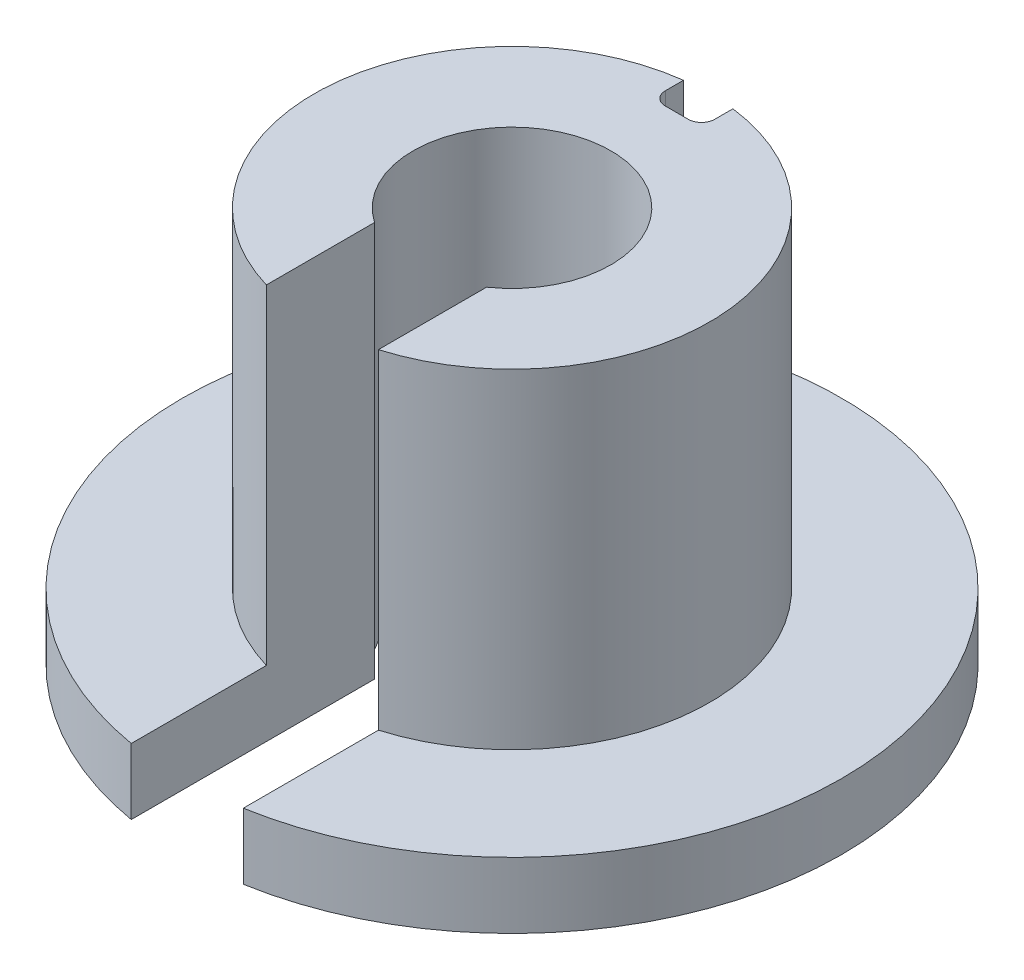
SolidWorks part; units mm, degrees
ref_plane "Front Plane" through (0, 0, 0) normal (0, 0, 1) x (1, 0, 0)
ref_plane "Top Plane" through (0, 0, 0) normal (0, 1, 0) x (1, 0, 0)
ref_plane "Right Plane" through (0, 0, 0) normal (1, 0, 0) x (0, 0, -1)
sketch "Sketch1" plane through (0, 0, 0) normal (0, 1, 0) x (1, 0, 0)
  line L0 (0, 0) -> (0, -6.8016) construction
  line L2 (-1.7, -2.4718) -> (-1.7, -5.7541)
  line L4 (1.7, -2.4718) -> (1.7, -5.7541)
  arc A0 (1.7, -2.4718) -> (-1.7, -2.4718) centre (0, 0) ccw
  arc A1 (1.7, -5.7541) -> (-1.7, -5.7541) centre (0, 0) ccw
  circle A3 centre (0, 0) radius 3 construction
  circle A4 centre (0, 0) radius 6 construction
  point P1 (5.7378, 1.7542)
  point P8 (2.8689, 0.8771)
  dimension "D1" = 6
  dimension "D3" = 1.7
  dimension "D4" = 1.7
  dimension "D2" = 3
extrude "Boss-Extrude1" add sketch "Sketch1" along normal blind 12
sketch "Sketch2" plane through (0, 0, 0) normal (0, -1, 0) x (1, 0, 0)
  line L0 (-1.7, 5.7541) -> (-1.7, 9.8544)
  line L2 (1.7, 5.7541) -> (1.7, 9.8544)
  arc A0 (-1.7, 9.8544) -> (1.7, 9.8544) centre (0, 0) ccw
  arc A1 (-1.7, 5.7541) -> (1.7, 5.7541) centre (0, 0) ccw
  dimension "D1" = 20
extrude "Boss-Extrude2" add sketch "Sketch2" against normal blind 2
sketch "Sketch3" plane through (0, 12, 0) normal (0, 1, 0) x (1, 0, 0)
  line L0 (0, 0) -> (0, 6) construction
  line L2 (-0.75, 5.9529) -> (-0.75, 5)
  line L3 (-0.75, 5) -> (0.75, 5)
  line L4 (0.75, 5.9529) -> (0.75, 5)
  arc A0 (1.7, -5.7541) -> (-1.7, -5.7541) centre (0, 0) ccw construction
  arc A1 (0.75, 5.9529) -> (-0.75, 5.9529) centre (0, 0) ccw
  dimension "D1" = 1.5
  dimension "D2" = 0.75
  dimension "D3" = 1
extrude "Cut-Extrude1" cut sketch "Sketch3" against normal up to surface (10 mm away) up to face at (0, 2, -0.0979)
fillet "Fillet1" radius 0.4 2 edges at (0.75, 7, -5) (-0.75, 7, -5)
